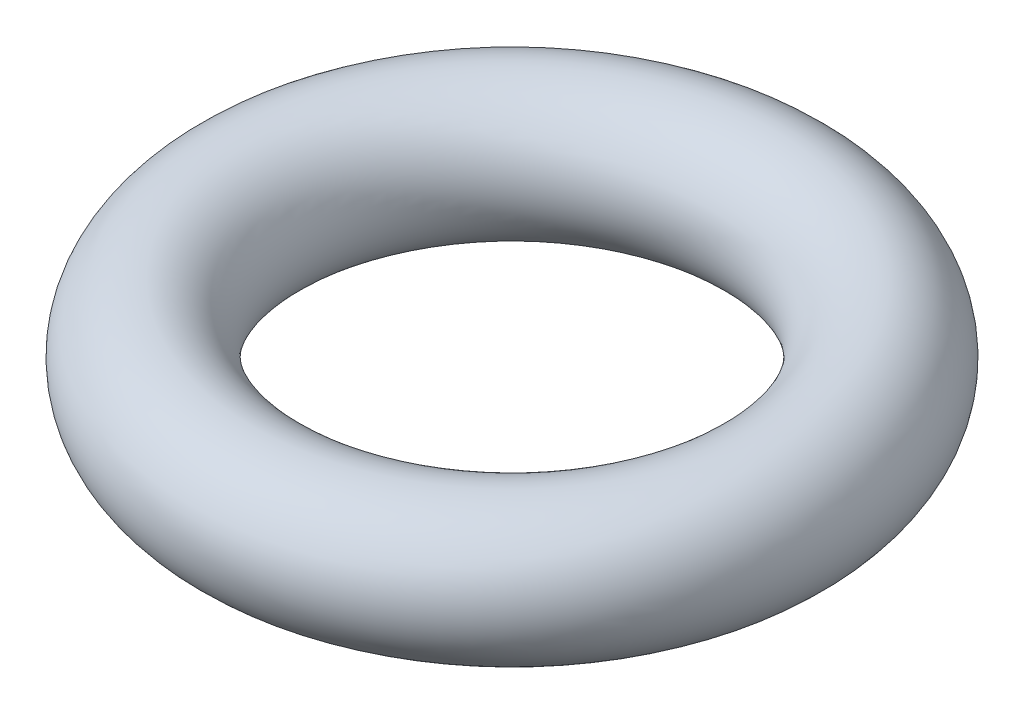
SolidWorks part; units mm, degrees
ref_plane "Front Plane" through (0, 0, 0) normal (0, 0, 1) x (1, 0, 0)
ref_plane "Top Plane" through (0, 0, 0) normal (0, 1, 0) x (1, 0, 0)
ref_plane "Right Plane" through (0, 0, 0) normal (1, 0, 0) x (0, 0, -1)
sketch "Sketch1" plane through (0, 0, 0) normal (0, 0, 1) x (1, 0, 0)
  line L0 (0, 1.25) -> (0, -1.25) construction
  circle A0 centre (4.75, 0) radius 1.25
revolve "Revolve1" add sketch "Sketch1" angle 360 about L0
